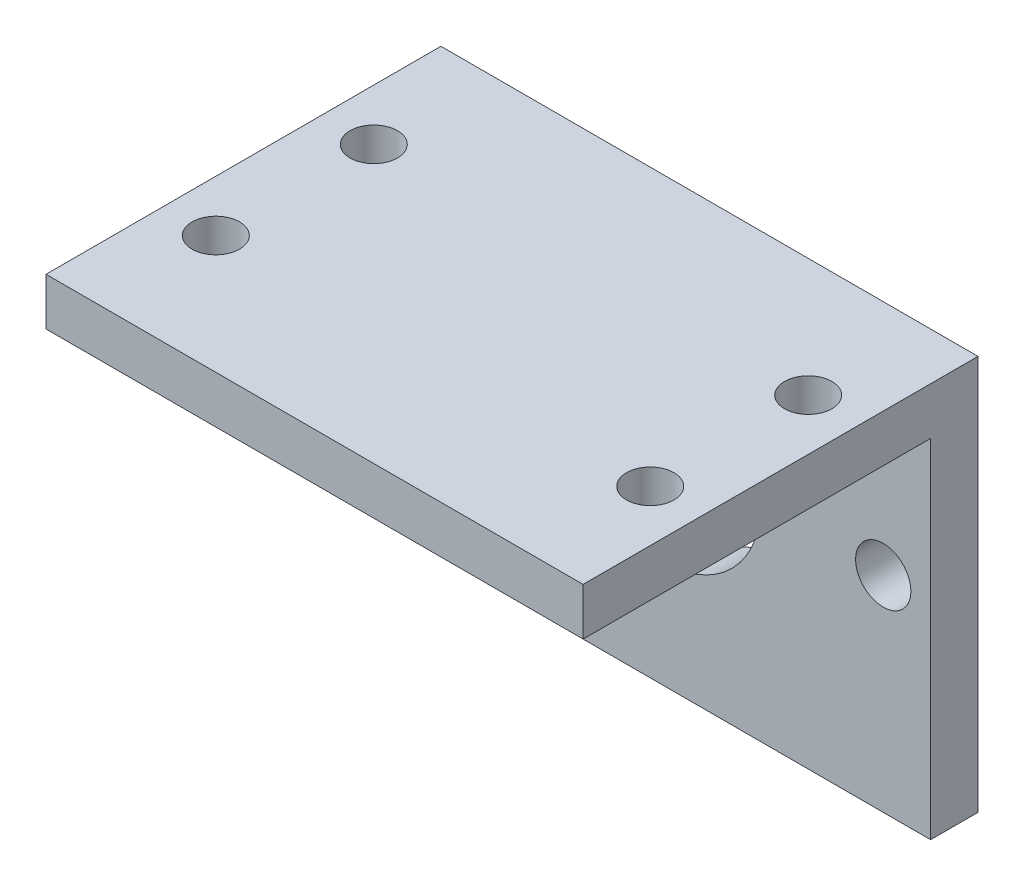
SolidWorks part; units mm, degrees
material "6061 合金"
ref_plane "前视基准面" through (0, 0, 0) normal (0, 0, 1) x (1, 0, 0)
ref_plane "上视基准面" through (0, 0, 0) normal (0, 1, 0) x (1, 0, 0)
ref_plane "右视基准面" through (0, 0, 0) normal (1, 0, 0) x (0, 0, -1)
sketch "草图1" plane through (0, 0, 0) normal (0, 1, 0) x (1, 0, 0)
  line L0 (0, 0) -> (0, 76.0239) construction
  line L1 (0, 0) -> (50.0233, 0) construction
  line L2 (-34, 50) -> (34, 50)
  line L3 (-34, 50) -> (-34, 0)
  line L4 (-34, 0) -> (34, 0)
  line L5 (34, 50) -> (34, 0)
  line L7 (-27.5, 35) -> (27.5, 35) construction
  line L8 (-27.5, 35) -> (-27.5, 15) construction
  line L9 (-27.5, 15) -> (27.5, 15) construction
  line L10 (27.5, 35) -> (27.5, 15) construction
  circle A0 centre (-27.5, 35) radius 3
  circle A1 centre (27.5, 35) radius 3
  circle A2 centre (-27.5, 15) radius 3
  circle A3 centre (27.5, 15) radius 3
  dimension "D6" = 6
  dimension "D7" = 6
  dimension "D8" = 6
  dimension "D9" = 6
  dimension "D1" = 68
  dimension "D2" = 50
  dimension "D3" = 55
  dimension "D4" = 20
  dimension "D5" = 15
extrude "凸台-拉伸1" add sketch "草图1" along normal blind 6
sketch "草图3" plane through (0, 6, 0) normal (0, 1, 0) x (1, 0, 0)
  line L0 (-34, 50) -> (-34, 0) construction
  line L1 (-34, 50) -> (34, 50)
  line L2 (-34, 50) -> (-34, 44)
  line L3 (-34, 44) -> (34, 44)
  line L4 (34, 50) -> (34, 44)
  line L5 (34, 50) -> (-34, 50) construction
  dimension "D1" = 68
  dimension "D2" = 6
extrude "凸台-拉伸2" add sketch "草图3" against normal blind 50
sketch "草图4" plane through (0, 0, -44) normal (0, 0, 1) x (1, 0, 0)
  line L0 (0, 0) -> (0, -44) construction
  line L1 (-34, -44) -> (34, -44) construction
  line L2 (0, -18) -> (28, -18) construction
  line L4 (34, 6) -> (-34, 6) construction
  circle A0 centre (0, -18) radius 12.5
  circle A1 centre (28, -18) radius 3.5
  circle A2 centre (-28, -18) radius 3.5
  dimension "D1" = 25
  dimension "D2" = 24
  dimension "D3" = 7
extrude "切除-拉伸1" cut sketch "草图4" against normal up to next
